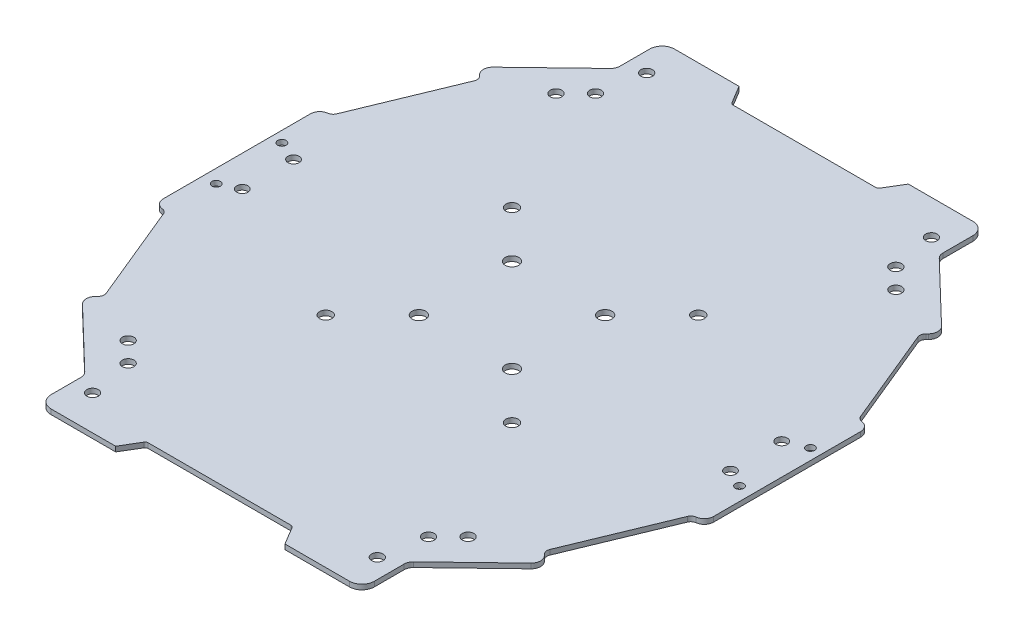
SolidWorks part; units mm, degrees
ref_plane "Front Plane" through (0, 0, 0) normal (0, 0, 1) x (1, 0, 0)
ref_plane "Top Plane" through (0, 0, 0) normal (0, 1, 0) x (1, 0, 0)
ref_plane "Right Plane" through (0, 0, 0) normal (1, 0, 0) x (0, 0, -1)
ref_plane "Plane1"
sketch "Sketch1" plane through (0, 0, 0) normal (0, 1, 0) x (-1, 0, 0)
  line L0 (74.0875, 321.0883) -> (70.3692, 327.2855)
  line L1 (70.3692, 327.2855) -> (45.5805, 327.2855)
  line L2 (45.5805, 327.2855) -> (45.5805, 312.4122)
  line L3 (45.5805, 312.4122) -> (23.246, 290.9343)
  line L4 (23.246, 290.9343) -> (26.6825, 287.3608)
  line L5 (26.6825, 287.3608) -> (12.7354, 253.539)
  line L6 (12.7354, 253.539) -> (9.0171, 253.539)
  line L7 (9.0171, 253.539) -> (9.0171, 226.8911)
  line L8 (9.0171, 226.8911) -> (9.0171, 200.2432)
  line L9 (9.0171, 200.2432) -> (12.7354, 200.2432)
  line L10 (12.7354, 200.2432) -> (26.6825, 166.4214)
  line L11 (26.6825, 166.4214) -> (23.246, 162.8479)
  line L12 (23.246, 162.8479) -> (45.5805, 141.37)
  line L13 (45.5805, 141.37) -> (45.5805, 126.4967)
  line L14 (45.5805, 126.4967) -> (70.3692, 126.4967)
  line L15 (70.3692, 126.4967) -> (74.0875, 132.6939)
  line L16 (74.0875, 132.6939) -> (97.6368, 132.6939)
  line L17 (97.6368, 132.6939) -> (121.1861, 132.6939)
  line L18 (121.1861, 132.6939) -> (124.9044, 126.4967)
  line L19 (124.9044, 126.4967) -> (149.6932, 126.4967)
  line L20 (149.6932, 126.4967) -> (149.6932, 141.37)
  line L21 (149.6932, 141.37) -> (172.0276, 162.8479)
  line L22 (172.0276, 162.8479) -> (168.5911, 166.4214)
  line L23 (168.5911, 166.4214) -> (182.5382, 200.2432)
  line L24 (182.5382, 200.2432) -> (186.2565, 200.2432)
  line L25 (186.2565, 200.2432) -> (186.2565, 226.8911)
  line L26 (186.2565, 226.8911) -> (186.2565, 253.539)
  line L27 (186.2565, 253.539) -> (182.5382, 253.539)
  line L28 (182.5382, 253.539) -> (168.5911, 287.3608)
  line L29 (168.5911, 287.3608) -> (172.0276, 290.9343)
  line L30 (172.0276, 290.9343) -> (149.6932, 312.4122)
  line L31 (149.6932, 312.4122) -> (149.6932, 327.2855)
  line L32 (149.6932, 327.2855) -> (124.9044, 327.2855)
  line L33 (124.9044, 327.2855) -> (121.1861, 321.0883)
  line L34 (121.1861, 321.0883) -> (97.6368, 321.0883)
  line L35 (97.6368, 321.0883) -> (74.0875, 321.0883)
  line L36 (97.6368, 132.6939) -> (97.6368, 321.0883) construction
  line L37 (9.0171, 226.8911) -> (186.2565, 226.8911) construction
  line L38 (67.6368, 256.8911) -> (127.6368, 196.8911) construction
  line L39 (127.6368, 256.8911) -> (67.6368, 196.8911) construction
  line L40 (42.8881, 295.782) -> (49.2662, 302.1601) construction
  line L41 (146.0075, 302.1601) -> (152.3856, 295.782) construction
  line L42 (49.2662, 151.6221) -> (42.8881, 158.0002) construction
  line L43 (146.0075, 151.6221) -> (152.3856, 158.0002) construction
  line L126 (176.3908, 226.8911) -> (176.3908, 225.1916)
  circle A0 centre (112.6368, 211.8911) radius 2.2
  circle A1 centre (49.2662, 151.6221) radius 1.8592
  circle A2 centre (112.6368, 241.8911) radius 2.2
  circle A3 centre (82.6368, 241.8911) radius 2.2
  circle A4 centre (82.6368, 211.8911) radius 2.2
  circle A8 centre (176.2565, 218.6411) radius 1.8
  circle A9 centre (176.2565, 235.1411) radius 1.8
  circle A10 centre (19.0171, 218.6411) radius 1.8
  circle A11 centre (19.0171, 235.1411) radius 1.8
  circle A12 centre (182.7565, 215.8911) radius 1.35
  circle A13 centre (181.9185, 237.8911) radius 1.35
  circle A22 centre (51.7777, 316.1305) radius 1.8592
  circle A23 centre (49.2662, 302.1601) radius 1.8592
  circle A24 centre (13.3551, 237.8911) radius 1.35
  circle A27 centre (143.496, 137.6517) radius 1.8592
  circle A28 centre (146.0075, 151.6221) radius 1.8592
  circle A30 centre (143.496, 316.1305) radius 1.8592
  circle A54 centre (146.0075, 302.1601) radius 1.8592
  circle A74 centre (12.5171, 215.8911) radius 1.35
  circle A77 centre (51.7777, 137.6517) radius 1.8592
  circle A78 centre (67.6368, 196.8911) radius 1.9831
  circle A79 centre (67.6368, 256.8911) radius 1.9831
  circle A82 centre (42.8881, 158.0002) radius 1.8592
  circle A86 centre (152.3856, 295.782) radius 1.8592
  circle A87 centre (42.8881, 295.782) radius 1.8592
  circle A90 centre (127.6368, 256.8911) radius 1.9831
  circle A91 centre (152.3856, 158.0002) radius 1.8592
  circle A96 centre (127.6368, 196.8911) radius 1.9831
  dimension "D1" = 30
  dimension "D11" = 15
  dimension "D14" = 3.5
  dimension "D28" = 6.1972
  dimension "D32" = 11
  dimension "D2" = 30
  dimension "D3" = 30
  dimension "D4" = 30
  dimension "D5" = 15
  dimension "D6" = 15
  dimension "D7" = 30
  dimension "D8" = 30
  dimension "D9" = 30
  dimension "D10" = 30
  dimension "D12" = 30
  dimension "D13" = 15
  dimension "D15" = 22
  dimension "D16" = 9.02
  dimension "D17" = 9.02
  dimension "D18" = 9.02
  dimension "D19" = 9.02
  dimension "D20" = 10
  dimension "D21" = 10
  dimension "D22" = 10
  dimension "D23" = 10
  dimension "D24" = 45
  dimension "D25" = 45
  dimension "D26" = 45
  dimension "D27" = 45
  dimension "D29" = 10
  dimension "D30" = 16.5
  dimension "D31" = 8.25
extrude "Extrusion1" add sketch "Sketch1" along normal blind 1.6
fillet "Fillet1" radius 1 4 edges at (-121.1861, 0.8, 132.6939) (-74.0875, 0.8, 132.6939) (-74.0875, 0.8, 321.0883) (-121.1861, 0.8, 321.0883)
fillet "Fillet2" radius 4 4 edges at (-149.6932, 0.8, 126.4967) (-45.5805, 0.8, 126.4967) (-149.6932, 0.8, 327.2855) (-45.5805, 0.8, 327.2855)
fillet "Fillet3" radius 3 4 edges at (-149.6932, 0.8, 141.37) (-45.5805, 0.8, 141.37) (-45.5805, 0.8, 312.4122) (-149.6932, 0.8, 312.4122)
fillet "Fillet4" radius 3 1 edges at (-172.0276, 0.8, 290.9343)
fillet "Fillet5" radius 2 1 edges at (-168.5911, 0.8, 287.3608)
fillet "Fillet6" radius 2 1 edges at (-26.6825, 0.8, 287.3608)
fillet "Fillet7" radius 3 1 edges at (-23.246, 0.8, 290.9343)
fillet "Fillet8" radius 3 2 edges at (-172.0276, 0.8, 162.8479) (-23.246, 0.8, 162.8479)
fillet "Fillet9" radius 2 2 edges at (-26.6825, 0.8, 166.4214) (-168.5911, 0.8, 166.4214)
fillet "Fillet10" radius 2 4 edges at (-12.7354, 0.8, 200.2432) (-12.7354, 0.8, 253.539) (-182.5382, 0.8, 253.539) (-182.5382, 0.8, 200.2432)
fillet "Fillet11" radius 3 4 edges at (-186.2565, 0.8, 200.2432) (-186.2565, 0.8, 253.539) (-9.0171, 0.8, 253.539) (-9.0171, 0.8, 200.2432)
